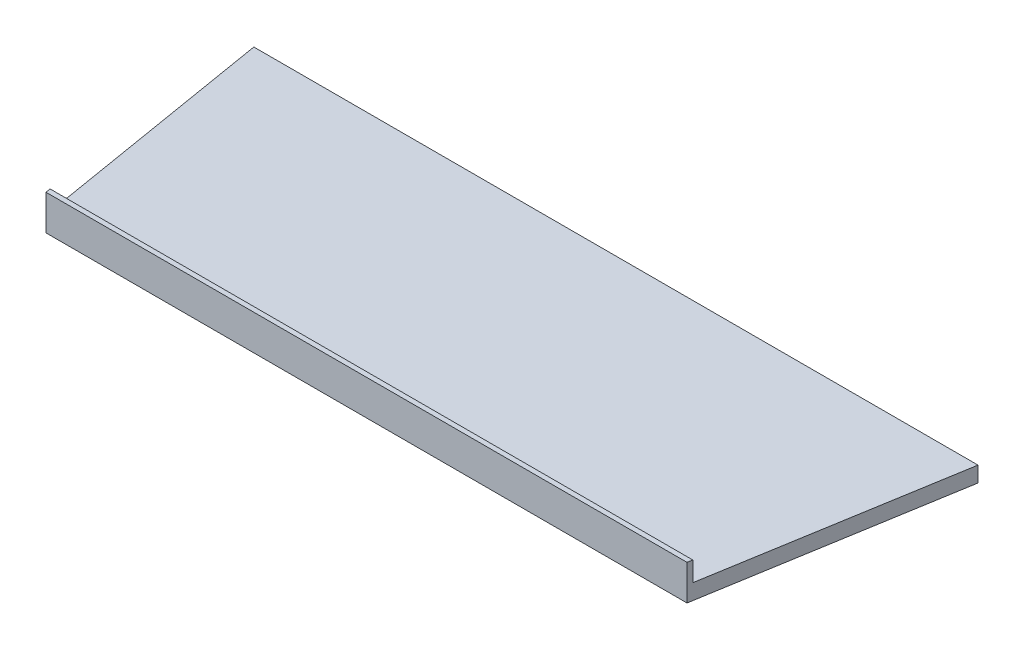
SolidWorks part; units mm, degrees
ref_plane "Front" through (0, 0, 0) normal (0, 0, 1) x (1, 0, 0)
ref_plane "Top" through (0, 0, 0) normal (0, 1, 0) x (1, 0, 0)
ref_plane "Right" through (0, 0, 0) normal (1, 0, 0) x (0, 0, -1)
sketch "Sketch1" plane through (0, 0, 0) normal (0, 1, 0) x (1, 0, 0)
  line L0 (-223.1356, -77.6924) -> (-248.5356, 74.7076)
  line L1 (-248.5356, 74.7076) -> (218.1894, 74.7076)
  line L2 (218.1894, 74.7076) -> (192.7894, -77.6924)
  line L3 (192.7894, -77.6924) -> (-223.1356, -77.6924)
  line L4 (-230.2091, -86.0424) -> (-258.3924, 83.0576)
  line L5 (-258.3924, 83.0576) -> (228.0462, 83.0576)
  line L6 (228.0462, 83.0576) -> (199.8629, -86.0424)
  line L7 (199.8629, -86.0424) -> (-230.2091, -86.0424)
  line L8 (-223.1356, -77.6924) -> (-221.7439, -86.0424)
  line L9 (192.7894, -77.6924) -> (191.3977, -86.0424)
  dimension "D1" = 466.725
  dimension "D2" = 415.925
  dimension "D3" = 152.4
  dimension "D4" = 8.35
extrude "Boss-Extrude1" add sketch "Sketch1" along normal blind 10 contours L9 L3 L8 L7
sketch "Sketch2" plane through (0, 10, 0) normal (0, 1, 0) x (1, 0, 0)
  line L0 (-221.7439, -86.0424) -> (191.3977, -86.0424)
  line L1 (191.3977, -86.0424) -> (191.9269, -82.8674)
  line L2 (218.1894, 74.7076) -> (191.3977, -86.0424) construction
  line L3 (191.9269, -82.8674) -> (-222.2731, -82.8674)
  line L4 (-248.5356, 74.7076) -> (-221.7439, -86.0424) construction
  line L5 (-222.2731, -82.8674) -> (-221.7439, -86.0424)
  dimension "D1" = 3.175
extrude "Boss-Extrude2" add sketch "Sketch2" along normal blind 12.7
